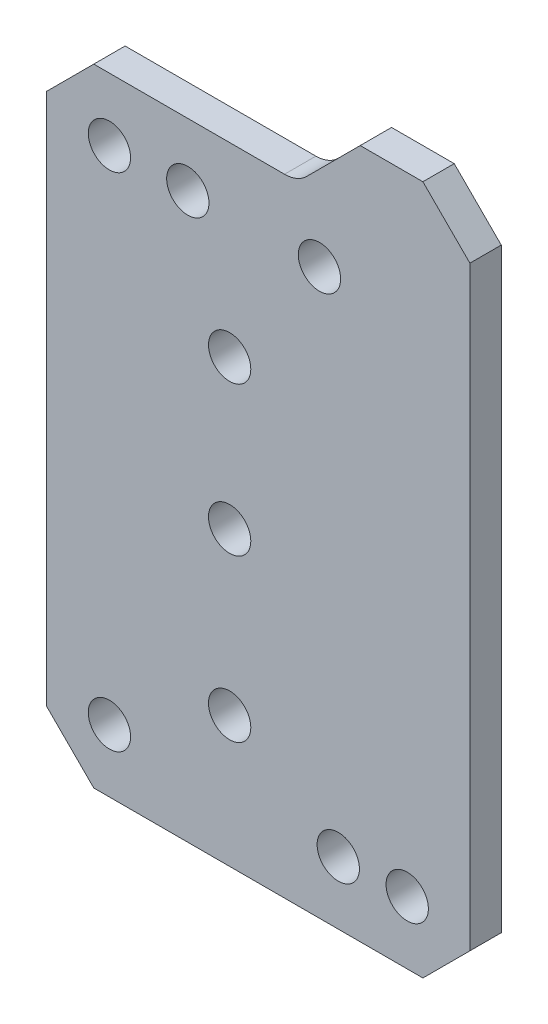
SolidWorks part; units mm, degrees
ref_plane "Спереди" through (0, 0, 0) normal (0, 0, 1) x (1, 0, 0)
ref_plane "Сверху" through (0, 0, 0) normal (0, 1, 0) x (1, 0, 0)
ref_plane "Справа" through (0, 0, 0) normal (1, 0, 0) x (0, 0, -1)
sketch "Эскиз1" plane through (0, 0, 0) normal (0, 0, 1) x (1, 0, 0)
  line L8 (469.8985, 620) -> (469.8985, 450)
  line L9 (469.8985, 450) -> (484.8985, 435)
  line L10 (484.8985, 435) -> (589.8985, 435)
  line L11 (589.8985, 435) -> (604.8985, 450)
  line L12 (604.8985, 450) -> (604.8985, 640)
  line L13 (604.8985, 640) -> (589.8985, 655)
  line L14 (589.8985, 655) -> (569.8985, 655)
  line L15 (545.7564, 635) -> (484.8985, 635)
  line L16 (469.8985, 620) -> (469.8985, 450)
  line L17 (469.8985, 450) -> (484.8985, 435)
  line L18 (484.8985, 435) -> (589.8985, 435)
  line L19 (589.8985, 435) -> (604.8985, 450)
  line L20 (604.8985, 450) -> (604.8985, 640)
  line L21 (604.8985, 640) -> (589.8985, 655)
  line L22 (589.8985, 655) -> (569.8985, 655)
  line L23 (545.7564, 635) -> (484.8985, 635)
  line L92 (484.8985, 635) -> (469.8985, 620)
  line L93 (484.8985, 635) -> (469.8985, 620)
  line L94 (569.8985, 655) -> (552.8275, 637.9289)
  line L95 (569.8985, 655) -> (552.8275, 637.9289)
  circle A0 centre (584.8985, 455) radius 6.75
  circle A1 centre (562.8985, 455) radius 6.75
  circle A2 centre (489.8985, 455) radius 6.75
  circle A3 centre (528.2461, 476.7497) radius 6.75
  circle A4 centre (528.2461, 528.2497) radius 6.75
  circle A5 centre (528.2461, 575.7497) radius 6.75
  circle A6 centre (514.8985, 615) radius 6.75
  circle A7 centre (489.8985, 615) radius 6.75
  circle A8 centre (556.8985, 615) radius 6.75
  circle A9 centre (528.2461, 476.7497) radius 6.75 construction
  circle A10 centre (528.2461, 528.2497) radius 6.5 construction
  circle A11 centre (528.2461, 575.7497) radius 6.75 construction
  arc A14 (545.7564, 635) -> (552.8275, 637.9289) centre (545.7564, 645) ccw
  arc A15 (545.7564, 635) -> (552.8275, 637.9289) centre (545.7564, 645) ccw
  dimension "D2" = 13.5
  dimension "D1" = 0
extrude "Бобышка-Вытянуть1" add sketch "Эскиз1" along normal blind 10
